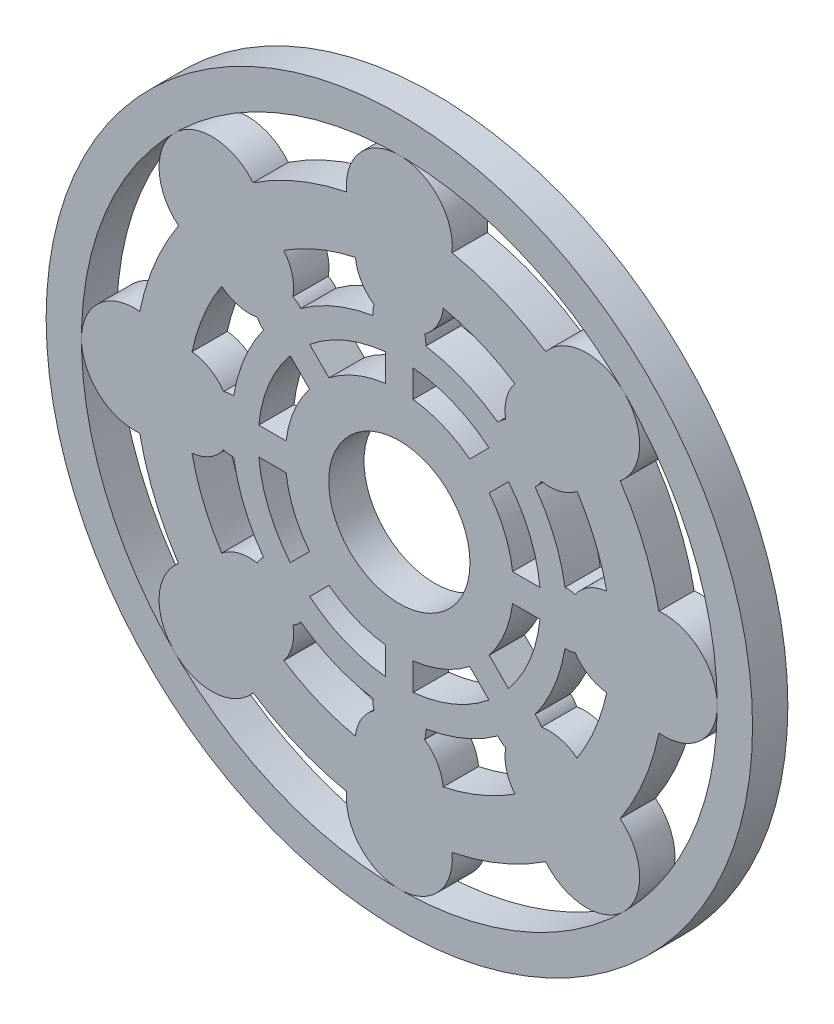
SolidWorks part; units mm, degrees
ref_plane "Front Plane" through (0, 0, 0) normal (0, 0, 1) x (1, 0, 0)
ref_plane "Top Plane" through (0, 0, 0) normal (0, 1, 0) x (1, 0, 0)
ref_plane "Right Plane" through (0, 0, 0) normal (1, 0, 0) x (0, 0, -1)
sketch "Sketch1" plane through (0, 0, 0) normal (0, 0, 1) x (1, 0, 0)
  line L0 (-31.8228, -26.2982) -> (-25.4327, -19.9081)
  line L1 (-26.2982, -31.8228) -> (-19.9081, -25.4327)
  line L2 (-3.9065, -41.0977) -> (-3.9065, -32.0608)
  line L3 (-41.0977, 3.9065) -> (-32.0608, 3.9065)
  line L4 (3.9065, -41.0977) -> (3.9065, -32.0608)
  line L5 (-41.0977, -3.9065) -> (-32.0608, -3.9065)
  line L6 (-26.2982, 31.8228) -> (-19.9081, 25.4327)
  line L7 (-31.8228, 26.2982) -> (-25.4327, 19.9081)
  line L8 (3.9065, 41.0977) -> (3.9065, 32.0608)
  line L9 (-3.9065, 41.0977) -> (-3.9065, 32.0608)
  line L10 (31.8228, 26.2982) -> (25.4327, 19.9081)
  line L11 (26.2982, 31.8228) -> (19.9081, 25.4327)
  line L12 (41.0977, -3.9065) -> (32.0608, -3.9065)
  line L13 (41.0977, 3.9065) -> (32.0608, 3.9065)
  line L14 (26.2982, -31.8228) -> (19.9081, -25.4327)
  line L15 (31.8228, -26.2982) -> (25.4327, -19.9081)
  circle A0 centre (0, 0) radius 100
  arc A1 (73.5, 14.9248) -> (62.5258, 41.4189) centre (0, 0) ccw
  arc A2 (65.2083, -11.3632) -> (65.2083, 11.3632) centre (75, 0) ccw
  arc A3 (49.75, -7.1545) -> (65.2083, -11.3632) centre (60, 0) ccw
  arc A4 (49.75, 7.1545) -> (41.0977, 3.9065) centre (47.5, 0) ccw
  arc A5 (65.2083, 11.3632) -> (49.75, 7.1545) centre (60, 0) ccw
  circle A6 centre (0, 0) radius 90
  arc A7 (58.6979, 12.432) -> (50.2964, 32.7149) centre (0, 0) ccw
  circle A8 centre (0, 0) radius 20
  arc A9 (46.9079, 7.4766) -> (38.4556, 27.8821) centre (0, 0) ccw
  arc A10 (40.2376, -30.1195) -> (31.8228, -26.2982) centre (33.5876, -33.5876) ccw
  arc A11 (54.1443, -38.0742) -> (40.2376, -30.1195) centre (42.4264, -42.4264) ccw
  arc A12 (38.0742, -54.1443) -> (54.1443, -38.0742) centre (53.033, -53.033) ccw
  arc A13 (30.1195, -40.2376) -> (38.0742, -54.1443) centre (42.4264, -42.4264) ccw
  arc A14 (7.1545, -49.75) -> (3.9065, -41.0977) centre (0, -47.5) ccw
  arc A15 (11.3632, -65.2083) -> (7.1545, -49.75) centre (0, -60) ccw
  arc A16 (-11.3632, -65.2083) -> (11.3632, -65.2083) centre (0, -75) ccw
  arc A17 (-7.1545, -49.75) -> (-11.3632, -65.2083) centre (0, -60) ccw
  arc A18 (-30.1195, -40.2376) -> (-26.2982, -31.8228) centre (-33.5876, -33.5876) ccw
  arc A19 (-38.0742, -54.1443) -> (-30.1195, -40.2376) centre (-42.4264, -42.4264) ccw
  arc A20 (-54.1443, -38.0742) -> (-38.0742, -54.1443) centre (-53.033, -53.033) ccw
  arc A21 (-40.2376, -30.1195) -> (-54.1443, -38.0742) centre (-42.4264, -42.4264) ccw
  arc A22 (-49.75, -7.1545) -> (-41.0977, -3.9065) centre (-47.5, 0) ccw
  arc A23 (-65.2083, -11.3632) -> (-49.75, -7.1545) centre (-60, 0) ccw
  arc A24 (-65.2083, 11.3632) -> (-65.2083, -11.3632) centre (-75, 0) ccw
  arc A25 (-49.75, 7.1545) -> (-65.2083, 11.3632) centre (-60, 0) ccw
  arc A26 (-40.2376, 30.1195) -> (-31.8228, 26.2982) centre (-33.5876, 33.5876) ccw
  arc A27 (-54.1443, 38.0742) -> (-40.2376, 30.1195) centre (-42.4264, 42.4264) ccw
  arc A28 (-38.0742, 54.1443) -> (-54.1443, 38.0742) centre (-53.033, 53.033) ccw
  arc A29 (-30.1195, 40.2376) -> (-38.0742, 54.1443) centre (-42.4264, 42.4264) ccw
  arc A30 (-7.1545, 49.75) -> (-3.9065, 41.0977) centre (0, 47.5) ccw
  arc A31 (-11.3632, 65.2083) -> (-7.1545, 49.75) centre (0, 60) ccw
  arc A32 (11.3632, 65.2083) -> (-11.3632, 65.2083) centre (0, 75) ccw
  arc A33 (7.1545, 49.75) -> (11.3632, 65.2083) centre (0, 60) ccw
  arc A34 (30.1195, 40.2376) -> (26.2982, 31.8228) centre (33.5876, 33.5876) ccw
  arc A35 (38.0742, 54.1443) -> (30.1195, 40.2376) centre (42.4264, 42.4264) ccw
  arc A36 (54.1443, 38.0742) -> (38.0742, 54.1443) centre (53.033, 53.033) ccw
  arc A37 (40.2376, 30.1195) -> (54.1443, 38.0742) centre (42.4264, 42.4264) ccw
  arc A38 (-73.5, -14.9248) -> (-62.5258, -41.4189) centre (0, 0) ccw
  arc A39 (-58.6979, -12.432) -> (-50.2964, -32.7149) centre (0, 0) ccw
  arc A40 (-46.9079, -7.4766) -> (-38.4556, -27.8821) centre (0, 0) ccw
  arc A41 (-62.5258, 41.4189) -> (-73.5, 14.9248) centre (0, 0) ccw
  arc A42 (-50.2964, 32.7149) -> (-58.6979, 12.432) centre (0, 0) ccw
  arc A43 (-38.4556, 27.8821) -> (-46.9079, 7.4766) centre (0, 0) ccw
  arc A44 (-14.9248, 73.5) -> (-41.4189, 62.5258) centre (0, 0) ccw
  arc A45 (-12.432, 58.6979) -> (-32.7149, 50.2964) centre (0, 0) ccw
  arc A46 (-7.4766, 46.9079) -> (-27.8821, 38.4556) centre (0, 0) ccw
  arc A47 (41.4189, 62.5258) -> (14.9248, 73.5) centre (0, 0) ccw
  arc A48 (32.7149, 50.2964) -> (12.432, 58.6979) centre (0, 0) ccw
  arc A49 (27.8821, 38.4556) -> (7.4766, 46.9079) centre (0, 0) ccw
  arc A50 (62.5258, -41.4189) -> (73.5, -14.9248) centre (0, 0) ccw
  arc A51 (50.2964, -32.7149) -> (58.6979, -12.432) centre (0, 0) ccw
  arc A52 (38.4556, -27.8821) -> (46.9079, -7.4766) centre (0, 0) ccw
  arc A53 (7.4766, -46.9079) -> (27.8821, -38.4556) centre (0, 0) ccw
  arc A54 (12.432, -58.6979) -> (32.7149, -50.2964) centre (0, 0) ccw
  arc A55 (14.9248, -73.5) -> (41.4189, -62.5258) centre (0, 0) ccw
  arc A56 (-41.4189, -62.5258) -> (-14.9248, -73.5) centre (0, 0) ccw
  arc A57 (-32.7149, -50.2964) -> (-12.432, -58.6979) centre (0, 0) ccw
  arc A58 (-27.8821, -38.4556) -> (-7.4766, -46.9079) centre (0, 0) ccw
  arc A59 (-3.9065, -41.0977) -> (-7.1545, -49.75) centre (0, -47.5) ccw
  circle A60 centre (0, 0) radius 32.2979
  arc A61 (3.9065, -39.8088) -> (25.3867, -30.9114) centre (0, 0) ccw
  arc A62 (-31.8228, -26.2982) -> (-40.2376, -30.1195) centre (-33.5876, -33.5876) ccw
  arc A63 (-25.3867, -30.9114) -> (-3.9065, -39.8088) centre (0, 0) ccw
  arc A64 (-41.0977, 3.9065) -> (-49.75, 7.1545) centre (-47.5, 0) ccw
  arc A65 (-39.8088, -3.9065) -> (-30.9114, -25.3867) centre (0, 0) ccw
  arc A66 (-26.2982, 31.8228) -> (-30.1195, 40.2376) centre (-33.5876, 33.5876) ccw
  arc A67 (-30.9114, 25.3867) -> (-39.8088, 3.9065) centre (0, 0) ccw
  arc A68 (3.9065, 41.0977) -> (7.1545, 49.75) centre (0, 47.5) ccw
  arc A69 (-3.9065, 39.8088) -> (-25.3867, 30.9114) centre (0, 0) ccw
  arc A70 (31.8228, 26.2982) -> (40.2376, 30.1195) centre (33.5876, 33.5876) ccw
  arc A71 (25.3867, 30.9114) -> (3.9065, 39.8088) centre (0, 0) ccw
  arc A72 (41.0977, -3.9065) -> (49.75, -7.1545) centre (47.5, 0) ccw
  arc A73 (39.8088, 3.9065) -> (30.9114, 25.3867) centre (0, 0) ccw
  arc A74 (26.2982, -31.8228) -> (30.1195, -40.2376) centre (33.5876, -33.5876) ccw
  arc A75 (30.9114, -25.3867) -> (39.8088, -3.9065) centre (0, 0) ccw
  point P69 (0, 0)
  point P147 (0, 0)
  dimension "D1" = 200
  dimension "D2" = 150
  dimension "D3" = 30
  dimension "D4" = 25
  dimension "D5" = 15
  dimension "D7" = 40
  dimension "D6" = 8
  dimension "D8" = 8
extrude "Boss-Extrude1" add sketch "Sketch1" along normal blind 10
